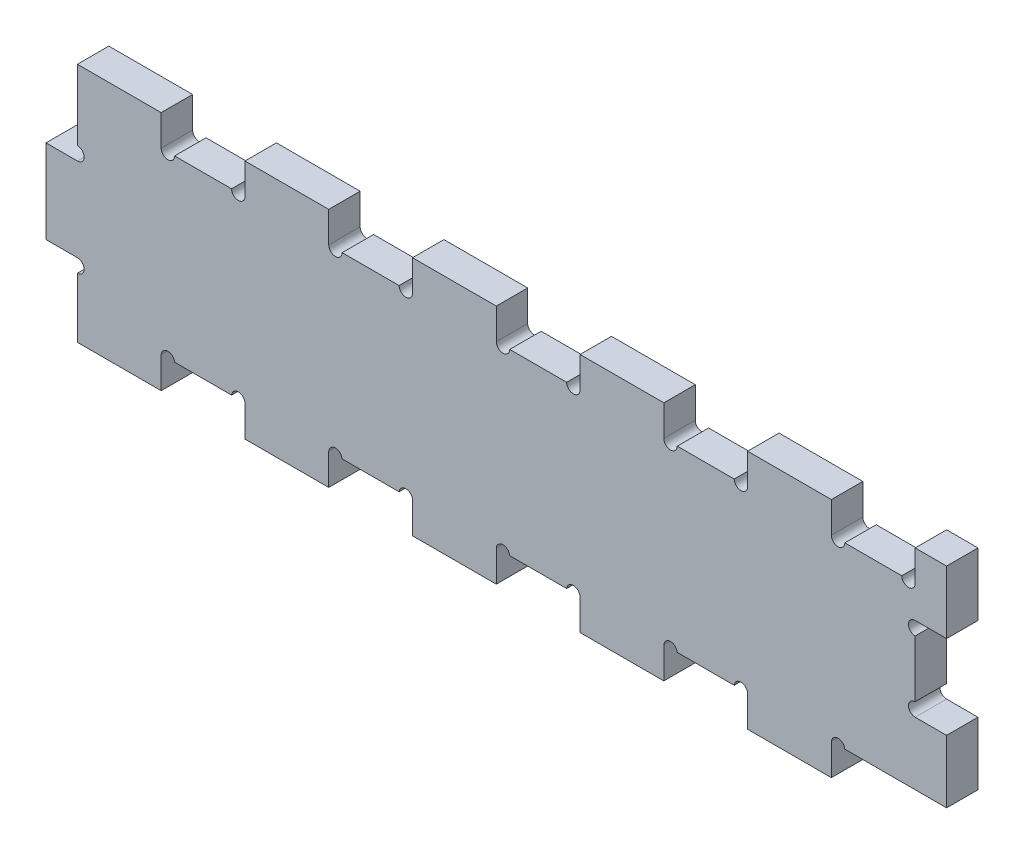
SolidWorks part; units mm, degrees
ref_plane "Alzado" through (0, 0, 0) normal (0, 0, 1) x (1, 0, 0)
ref_plane "Planta" through (0, 0, 0) normal (0, 1, 0) x (1, 0, 0)
ref_plane "Vista lateral" through (0, 0, 0) normal (1, 0, 0) x (0, 0, -1)
sketch "Croquis1" plane through (0, 0, 0) normal (0, 0, 1) x (1, 0, 0)
  line L1 (-200, -57.5) -> (-160, -57.5)
  line L2 (-215, -20) -> (-215, 20)
  line L3 (-200, 57.5) -> (-160, 57.5)
  line L5 (-215, -57.5) -> (215, 57.5) construction
  line L6 (-215, 57.5) -> (215, -57.5) construction
  line L7 (-215, 20) -> (-200, 20)
  line L9 (-215, -20) -> (-200, -20)
  line L11 (-230, 20) -> (-200, -20) construction
  line L12 (-230, -20) -> (-200, 20) construction
  line L13 (-200, 57.5) -> (-200, 26.4)
  line L14 (-160, -42.5) -> (-160, -49.3122)
  line L15 (-200, 57.5) -> (-160, 57.5)
  line L16 (-200, 57.5) -> (-200, 42.7907)
  line L18 (-160, 57.5) -> (-160, 42.7907)
  line L20 (-160, 42.7907) -> (-160, 57.5)
  line L22 (-120, 42.7907) -> (-120, 57.5)
  line L24 (-120, 42.7907) -> (-120, 57.5)
  line L25 (-120, 57.5) -> (-80, 57.5)
  line L26 (-80, 42.7907) -> (-80, 57.5)
  line L27 (-73.6, 42.7907) -> (-46.4, 42.7907)
  line L28 (-80, 42.7907) -> (-80, 57.5)
  line L30 (-40, 42.7907) -> (-40, 57.5)
  line L32 (-40, 42.7907) -> (-40, 57.5)
  line L33 (-40, 57.5) -> (0, 57.5)
  line L34 (0, 42.7907) -> (0, 57.5)
  line L36 (0, 57.5) -> (0, 42.7907)
  line L37 (6.4, 42.7907) -> (33.6, 42.7907)
  line L38 (40, 57.5) -> (40, 42.7907)
  line L40 (40, 42.7907) -> (40, 57.5)
  line L41 (40, 57.5) -> (80, 57.5)
  line L42 (80, 42.7907) -> (80, 57.5)
  line L43 (86.4, 42.7907) -> (113.6, 42.7907)
  line L44 (80, 42.7907) -> (80, 57.5)
  line L46 (120, 42.7907) -> (120, 57.5)
  line L48 (120, 42.7907) -> (120, 57.5)
  line L49 (120, 57.5) -> (160, 57.5)
  line L50 (160, 42.7907) -> (160, 57.5)
  line L51 (166.4, 42.7907) -> (193.6, 42.7907)
  line L52 (160, 42.7907) -> (160, 57.5)
  line L65 (215, 27.7907) -> (200, 27.7907)
  line L67 (215, 27.7907) -> (200, 27.7907)
  line L69 (215, -12.2093) -> (200, -12.2093)
  line L71 (200, -12.2093) -> (215, -12.2093)
  line L75 (160, -57.5) -> (120, -57.5)
  line L77 (200, -42.5) -> (166.3868, -42.5)
  line L78 (-200, -57.5) -> (-200, -42.5)
  line L79 (-120, 42.7907) -> (-120, 32.093)
  line L80 (-153.6, 42.7907) -> (-126.4, 42.7907)
  line L81 (-200, 26.4) -> (-200, 57.5)
  line L82 (-200, 23.2) -> (-200, 20)
  line L83 (40, 10.6977) -> (40, -10.6977)
  line L84 (80, 42.7907) -> (80, 21.3953)
  line L85 (120, 42.7907) -> (120, 32.093)
  line L86 (200, 42.7907) -> (200, 57.5)
  line L87 (-160, -49.3122) -> (-160, -57.5)
  line L88 (-160, -57.5) -> (-160.1599, -57.7146)
  line L89 (-80, -57.5) -> (-80, -42.5)
  line L90 (-120, -42.5) -> (-120, -57.5)
  line L91 (-40, -42.5) -> (-40, -57.5)
  line L92 (0, -42.5) -> (0, -57.5)
  line L93 (160, -42.5) -> (160, -57.5)
  line L94 (120, -42.5) -> (120, -57.5)
  line L95 (80, -42.5) -> (80, -57.5)
  line L96 (40, -42.5) -> (40, -57.5)
  line L97 (-200, -26.4) -> (-200, -57.5)
  line L98 (-120, 57.5) -> (-80, 57.5)
  line L99 (-40, 57.5) -> (0, 57.5)
  line L100 (40, 57.5) -> (80, 57.5)
  line L101 (120, 57.5) -> (160, 57.5)
  line L103 (200, -53.4884) -> (200, -57.5)
  line L105 (-120, -57.5) -> (-80, -57.5)
  line L106 (-160, -57.5) -> (-200, -57.5)
  line L107 (-120, -42.5) -> (-120.0132, -42.5)
  line L108 (-80, -57.5) -> (-120, -57.5)
  line L109 (-40, -57.5) -> (0, -57.5)
  line L110 (-40, -42.5) -> (-40.0132, -42.5)
  line L111 (0, -57.5) -> (-40, -57.5)
  line L112 (40, -57.5) -> (80, -57.5)
  line L113 (40, -42.5) -> (39.9868, -42.5)
  line L114 (80, -57.5) -> (40, -57.5)
  line L115 (120, -57.5) -> (160, -57.5)
  line L116 (120, -42.5) -> (119.9868, -42.5)
  line L117 (-200, 20) -> (-200, 23.2)
  line L118 (-215, 0) -> (-206.3098, 0)
  line L120 (-140, 42.7907) -> (-140, 32.6053)
  line L121 (-100, 57.5) -> (-100, 42.7907)
  line L122 (-20, 57.5) -> (-20, 37.3747)
  line L123 (140, 57.5) -> (140, 48.0923)
  line L124 (180, 33.8196) -> (180, 30.9199)
  line L126 (166.4, 42.7907) -> (193.6, 42.7907)
  line L127 (-158.913, -42.5) -> (-160, -42.5)
  line L128 (-126.3868, -42.5) -> (-153.6132, -42.5)
  line L129 (160, 57.5) -> (215, 57.5)
  line L130 (-79.9868, -42.5) -> (-80, -42.5)
  line L131 (-46.3868, -42.5) -> (-73.6132, -42.5)
  line L132 (0.0132, -42.5) -> (0, -42.5)
  line L133 (33.6132, -42.5) -> (6.3868, -42.5)
  line L134 (80.0132, -42.5) -> (80, -42.5)
  line L135 (113.6132, -42.5) -> (86.3868, -42.5)
  line L136 (120, -32.093) -> (120, -42.5)
  line L137 (160.0132, -42.5) -> (158.913, -42.5)
  line L141 (160, 57.5) -> (160, 42.7907)
  line L142 (200, 27.7907) -> (215, 27.7907)
  line L143 (215, 57.5) -> (215, 27.7907)
  line L144 (215, -12.2093) -> (200, -12.2093)
  line L145 (215, -12.2093) -> (215, -42.5)
  line L148 (200, -42.5) -> (215, -42.5)
  line L149 (200, -5.8093) -> (200, 21.3907)
  line L152 (200, 42.7907) -> (200, 33.8196)
  line L153 (200, 27.7907) -> (200, 24.5907)
  line L154 (200, 7.7907) -> (196.8, 7.7907)
  arc A0 (-200, 20) -> (-200, 26.4) centre (-200, 23.2) ccw
  arc A1 (-200, -20) -> (-200, -26.4) centre (-200, -23.2) cw
  arc A2 (-160, 42.7907) -> (-153.6, 42.7907) centre (-156.8, 42.7907) ccw
  arc A3 (-120, 42.7907) -> (-126.4, 42.7907) centre (-123.2, 42.7907) cw
  arc A4 (-80, 42.7907) -> (-73.6, 42.7907) centre (-76.8, 42.7907) ccw
  arc A5 (-40, 42.7907) -> (-46.4, 42.7907) centre (-43.2, 42.7907) cw
  arc A6 (120, 42.7907) -> (113.6, 42.7907) centre (116.8, 42.7907) cw
  arc A7 (80, 42.7907) -> (86.4, 42.7907) centre (83.2, 42.7907) ccw
  arc A8 (40, 42.7907) -> (33.6, 42.7907) centre (36.8, 42.7907) cw
  arc A9 (0, 42.7907) -> (6.4, 42.7907) centre (3.2, 42.7907) ccw
  arc A10 (160, 42.7907) -> (166.4, 42.7907) centre (163.2, 42.7907) ccw
  arc A13 (160, -42.7907) -> (166.3868, -42.5) centre (163.2, -42.7907) cw
  arc A14 (120, -42.7907) -> (113.6132, -42.5) centre (116.8, -42.7907) ccw
  arc A15 (80, -42.7907) -> (86.3868, -42.5) centre (83.2, -42.7907) cw
  arc A16 (40, -42.7907) -> (33.6132, -42.5) centre (36.8, -42.7907) ccw
  arc A17 (0, -42.7907) -> (6.3868, -42.5) centre (3.2, -42.7907) cw
  circle A18 centre (-43.2, -42.7907) radius 3.2
  circle A19 centre (-76.8, -42.7907) radius 3.2
  arc A20 (-120, -42.7907) -> (-126.3868, -42.5) centre (-123.2, -42.7907) ccw
  arc A21 (-160, -42.7907) -> (-153.6132, -42.5) centre (-156.8, -42.7907) cw
  arc A22 (200, 42.7907) -> (193.6, 42.7907) centre (196.8, 42.7907) cw
  arc A23 (200, 27.7907) -> (200, 21.3907) centre (200, 24.5907) ccw
  arc A24 (200, -12.2093) -> (200, -5.8093) centre (200, -9.0093) cw
  point P0 (0, 0)
  point P6 (-215, 0)
  dimension "D1" = 115
  dimension "D2" = 430
  dimension "D3" = 40
  dimension "D4" = 30
  dimension "D5" = 40
  dimension "D6" = 40
  dimension "D7" = 40
  dimension "D8" = 40
  dimension "D9" = 40
  dimension "D10" = 40
  dimension "D11" = 40
  dimension "D12" = 40
  dimension "D13" = 40
  dimension "D14" = 40
  dimension "D15" = 3.2
  dimension "D16" = 40
  dimension "D17" = 3.2
  dimension "D18" = 15
  dimension "D19" = 3.2
extrude "Saliente-Extruir2" add sketch "Croquis1" along normal blind 10
sketch "Croquis3" plane through (0, 0, 10) normal (0, 0, 1) x (1, 0, 0)
  line L59 (119.9868, -42.5) -> (120, -42.5)
  line L60 (120, -42.5) -> (120, -57.5)
  line L61 (120, -57.5) -> (160, -57.5)
  line L62 (160, -57.5) -> (160, -42.5)
  line L63 (160, -42.5) -> (160.0132, -42.5)
  line L64 (166.3868, -42.5) -> (215, -42.5)
  line L65 (215, -42.5) -> (215, -12.2093)
  line L66 (215, -12.2093) -> (200, -12.2093)
  line L67 (200, -5.8093) -> (200, 21.3907)
  line L68 (200, 27.7907) -> (215, 27.7907)
  line L69 (215, 27.7907) -> (215, 57.5)
  line L70 (215, 57.5) -> (200, 57.5)
  line L71 (200, 57.5) -> (200, 42.7907)
  line L72 (193.6, 42.7907) -> (166.4, 42.7907)
  line L73 (160, 42.7907) -> (160, 57.5)
  line L74 (160, 57.5) -> (120, 57.5)
  line L75 (120, 57.5) -> (120, 42.7907)
  line L76 (113.6, 42.7907) -> (86.4, 42.7907)
  line L77 (80, 42.7907) -> (80, 57.5)
  line L78 (80, 57.5) -> (40, 57.5)
  line L79 (40, 57.5) -> (40, 42.7907)
  line L80 (33.6, 42.7907) -> (6.4, 42.7907)
  line L81 (0, 42.7907) -> (0, 57.5)
  line L82 (0, 57.5) -> (-40, 57.5)
  line L83 (-40, 57.5) -> (-40, 42.7907)
  line L84 (-46.4, 42.7907) -> (-73.6, 42.7907)
  line L85 (-80, 42.7907) -> (-80, 57.5)
  line L86 (-80, 57.5) -> (-120, 57.5)
  line L87 (-120, 57.5) -> (-120, 42.7907)
  line L88 (-126.4, 42.7907) -> (-153.6, 42.7907)
  line L89 (-160, 42.7907) -> (-160, 57.5)
  line L90 (-160, 57.5) -> (-200, 57.5)
  line L91 (-200, 57.5) -> (-200, 26.4)
  line L92 (-200, 20) -> (-215, 20)
  line L93 (-215, 20) -> (-215, -20)
  line L94 (-215, -20) -> (-200, -20)
  line L95 (-200, -26.4) -> (-200, -57.5)
  line L96 (-200, -57.5) -> (-160, -57.5)
  line L97 (-160, -57.5) -> (-160, -42.5)
  line L98 (-160, -42.5) -> (-159.9868, -42.5)
  line L99 (-153.6132, -42.5) -> (-126.3868, -42.5)
  line L100 (-120.0132, -42.5) -> (-120, -42.5)
  line L101 (-120, -42.5) -> (-120, -57.5)
  line L102 (-120, -57.5) -> (-80, -57.5)
  line L103 (-80, -57.5) -> (-80, -42.5)
  line L104 (-80, -42.5) -> (-79.9868, -42.5)
  line L105 (-73.6132, -42.5) -> (-46.3868, -42.5)
  line L106 (-40.0132, -42.5) -> (-40, -42.5)
  line L107 (-40, -42.5) -> (-40, -57.5)
  line L108 (-40, -57.5) -> (0, -57.5)
  line L109 (0, -57.5) -> (0, -42.5)
  line L110 (0, -42.5) -> (0.0132, -42.5)
  line L111 (6.3868, -42.5) -> (33.6132, -42.5)
  line L112 (39.9868, -42.5) -> (40, -42.5)
  line L113 (40, -42.5) -> (40, -57.5)
  line L114 (40, -57.5) -> (80, -57.5)
  line L115 (80, -57.5) -> (80, -42.5)
  line L116 (80, -42.5) -> (80.0132, -42.5)
  line L117 (86.3868, -42.5) -> (113.6132, -42.5)
  line L118 (119.9868, -42.5) -> (120, -42.5)
  line L119 (120, -42.5) -> (120, -57.5)
  line L120 (120, -57.5) -> (160, -57.5)
  line L121 (160, -57.5) -> (160, -42.5)
  line L122 (160, -42.5) -> (160.0132, -42.5)
  line L123 (166.3868, -42.5) -> (215, -42.5)
  line L124 (215, -42.5) -> (215, -12.2093)
  line L125 (215, -12.2093) -> (200, -12.2093)
  line L126 (200, -5.8093) -> (200, 21.3907)
  line L127 (200, 27.7907) -> (215, 27.7907)
  line L128 (215, 27.7907) -> (215, 57.5)
  line L129 (215, 57.5) -> (200, 57.5)
  line L130 (200, 57.5) -> (200, 42.7907)
  line L131 (193.6, 42.7907) -> (166.4, 42.7907)
  line L132 (160, 42.7907) -> (160, 57.5)
  line L133 (160, 57.5) -> (120, 57.5)
  line L134 (120, 57.5) -> (120, 42.7907)
  line L135 (113.6, 42.7907) -> (86.4, 42.7907)
  line L136 (80, 42.7907) -> (80, 57.5)
  line L137 (80, 57.5) -> (40, 57.5)
  line L138 (40, 57.5) -> (40, 42.7907)
  line L139 (33.6, 42.7907) -> (6.4, 42.7907)
  line L140 (0, 42.7907) -> (0, 57.5)
  line L141 (0, 57.5) -> (-40, 57.5)
  line L142 (-40, 57.5) -> (-40, 42.7907)
  line L143 (-46.4, 42.7907) -> (-73.6, 42.7907)
  line L144 (-80, 42.7907) -> (-80, 57.5)
  line L145 (-80, 57.5) -> (-120, 57.5)
  line L146 (-120, 57.5) -> (-120, 42.7907)
  line L147 (-126.4, 42.7907) -> (-153.6, 42.7907)
  line L148 (-160, 42.7907) -> (-160, 57.5)
  line L149 (-160, 57.5) -> (-200, 57.5)
  line L150 (-200, 57.5) -> (-200, 26.4)
  line L151 (-200, 20) -> (-215, 20)
  line L152 (-215, 20) -> (-215, -20)
  line L153 (-215, -20) -> (-200, -20)
  line L154 (-200, -26.4) -> (-200, -57.5)
  line L155 (-200, -57.5) -> (-160, -57.5)
  line L156 (-160, -57.5) -> (-160, -42.5)
  line L157 (-160, -42.5) -> (-159.9868, -42.5)
  line L158 (-153.6132, -42.5) -> (-126.3868, -42.5)
  line L159 (-120.0132, -42.5) -> (-120, -42.5)
  line L160 (-120, -42.5) -> (-120, -57.5)
  line L161 (-120, -57.5) -> (-80, -57.5)
  line L162 (-80, -57.5) -> (-80, -42.5)
  line L163 (-80, -42.5) -> (-79.9868, -42.5)
  line L164 (-73.6132, -42.5) -> (-46.3868, -42.5)
  line L165 (-40.0132, -42.5) -> (-40, -42.5)
  line L166 (-40, -42.5) -> (-40, -57.5)
  line L167 (-40, -57.5) -> (0, -57.5)
  line L168 (0, -57.5) -> (0, -42.5)
  line L169 (0, -42.5) -> (0.0132, -42.5)
  line L170 (6.3868, -42.5) -> (33.6132, -42.5)
  line L171 (39.9868, -42.5) -> (40, -42.5)
  line L172 (40, -42.5) -> (40, -57.5)
  line L173 (40, -57.5) -> (80, -57.5)
  line L174 (80, -57.5) -> (80, -42.5)
  line L175 (80, -42.5) -> (80.0132, -42.5)
  line L176 (86.3868, -42.5) -> (113.6132, -42.5)
  arc A23 (166.3868, -42.5) -> (160.0132, -42.5) centre (163.2, -42.7907) ccw
  arc A24 (200, -5.8093) -> (200, -12.2093) centre (200, -9.0093) ccw
  arc A25 (200, 27.7907) -> (200, 21.3907) centre (200, 24.5907) ccw
  arc A26 (193.6, 42.7907) -> (200, 42.7907) centre (196.8, 42.7907) ccw
  arc A27 (160, 42.7907) -> (166.4, 42.7907) centre (163.2, 42.7907) ccw
  arc A28 (113.6, 42.7907) -> (120, 42.7907) centre (116.8, 42.7907) ccw
  arc A29 (80, 42.7907) -> (86.4, 42.7907) centre (83.2, 42.7907) ccw
  arc A30 (33.6, 42.7907) -> (40, 42.7907) centre (36.8, 42.7907) ccw
  arc A31 (0, 42.7907) -> (6.4, 42.7907) centre (3.2, 42.7907) ccw
  arc A32 (-46.4, 42.7907) -> (-40, 42.7907) centre (-43.2, 42.7907) ccw
  arc A33 (-80, 42.7907) -> (-73.6, 42.7907) centre (-76.8, 42.7907) ccw
  arc A34 (-126.4, 42.7907) -> (-120, 42.7907) centre (-123.2, 42.7907) ccw
  arc A35 (-160, 42.7907) -> (-153.6, 42.7907) centre (-156.8, 42.7907) ccw
  arc A36 (-200, 20) -> (-200, 26.4) centre (-200, 23.2) ccw
  arc A37 (-200, -26.4) -> (-200, -20) centre (-200, -23.2) ccw
  arc A38 (-153.6132, -42.5) -> (-159.9868, -42.5) centre (-156.8, -42.7907) ccw
  arc A39 (-120.0132, -42.5) -> (-126.3868, -42.5) centre (-123.2, -42.7907) ccw
  arc A40 (-73.6132, -42.5) -> (-79.9868, -42.5) centre (-76.8, -42.7907) ccw
  arc A41 (-40.0132, -42.5) -> (-46.3868, -42.5) centre (-43.2, -42.7907) ccw
  arc A42 (6.3868, -42.5) -> (0.0132, -42.5) centre (3.2, -42.7907) ccw
  arc A43 (39.9868, -42.5) -> (33.6132, -42.5) centre (36.8, -42.7907) ccw
  arc A44 (86.3868, -42.5) -> (80.0132, -42.5) centre (83.2, -42.7907) ccw
  arc A45 (119.9868, -42.5) -> (113.6132, -42.5) centre (116.8, -42.7907) ccw
  arc A46 (166.3868, -42.5) -> (160.0132, -42.5) centre (163.2, -42.7907) ccw
  arc A47 (200, -5.8093) -> (200, -12.2093) centre (200, -9.0093) ccw
  arc A48 (200, 27.7907) -> (200, 21.3907) centre (200, 24.5907) ccw
  arc A49 (193.6, 42.7907) -> (200, 42.7907) centre (196.8, 42.7907) ccw
  arc A50 (160, 42.7907) -> (166.4, 42.7907) centre (163.2, 42.7907) ccw
  arc A51 (113.6, 42.7907) -> (120, 42.7907) centre (116.8, 42.7907) ccw
  arc A52 (80, 42.7907) -> (86.4, 42.7907) centre (83.2, 42.7907) ccw
  arc A53 (33.6, 42.7907) -> (40, 42.7907) centre (36.8, 42.7907) ccw
  arc A54 (0, 42.7907) -> (6.4, 42.7907) centre (3.2, 42.7907) ccw
  arc A55 (-46.4, 42.7907) -> (-40, 42.7907) centre (-43.2, 42.7907) ccw
  arc A56 (-80, 42.7907) -> (-73.6, 42.7907) centre (-76.8, 42.7907) ccw
  arc A57 (-126.4, 42.7907) -> (-120, 42.7907) centre (-123.2, 42.7907) ccw
  arc A58 (-160, 42.7907) -> (-153.6, 42.7907) centre (-156.8, 42.7907) ccw
  arc A59 (-200, 20) -> (-200, 26.4) centre (-200, 23.2) ccw
  arc A60 (-200, -26.4) -> (-200, -20) centre (-200, -23.2) ccw
  arc A61 (-153.6132, -42.5) -> (-159.9868, -42.5) centre (-156.8, -42.7907) ccw
  arc A62 (-120.0132, -42.5) -> (-126.3868, -42.5) centre (-123.2, -42.7907) ccw
  arc A63 (-73.6132, -42.5) -> (-79.9868, -42.5) centre (-76.8, -42.7907) ccw
  arc A64 (-40.0132, -42.5) -> (-46.3868, -42.5) centre (-43.2, -42.7907) ccw
  arc A65 (6.3868, -42.5) -> (0.0132, -42.5) centre (3.2, -42.7907) ccw
  arc A66 (39.9868, -42.5) -> (33.6132, -42.5) centre (36.8, -42.7907) ccw
  arc A67 (86.3868, -42.5) -> (80.0132, -42.5) centre (83.2, -42.7907) ccw
  arc A68 (119.9868, -42.5) -> (113.6132, -42.5) centre (116.8, -42.7907) ccw
  dimension "D1" = 0
extrude "Saliente-Extruir3" add sketch "Croquis3" along normal blind 5
sketch "Croquis4" plane through (0, 0, 15) normal (0, 0, 1) x (1, 0, 0)
  line L0 (-215, 20) -> (-215, -20) construction
  line L1 (-200, 57.5) -> (-215, 57.5)
  line L2 (-200, 57.5) -> (-200, 17.5)
  line L3 (-200, 17.5) -> (-215, 17.5)
  line L4 (-215, 57.5) -> (-215, 17.5)
  dimension "D1" = 40
extrude "Cortar-Extruir1" cut sketch "Croquis4" against normal blind 15
sketch "Croquis5" plane through (0, 0, 15) normal (0, 0, 1) x (1, 0, 0)
  line L0 (-200, -26.4) -> (-200, -57.5) construction
  line L1 (-215, 17.5) -> (-200, 17.5)
  line L2 (-215, 17.5) -> (-215, -22.5)
  line L3 (-215, -22.5) -> (-200, -22.5)
  line L4 (-200, 17.5) -> (-200, -22.5)
  dimension "D1" = 40
extrude "Saliente-Extruir4" add sketch "Croquis5" against normal blind 15
sketch "Croquis6" plane through (0, 0, 15) normal (0, 0, 1) x (1, 0, 0)
  line L0 (-200, -22.5) -> (-200, -20) construction
  line L1 (-200, -22.5) -> (-200, -20)
  line L2 (-200, -26.4) -> (-200, -22.5)
  line L3 (-200, 20) -> (-200, 26.4)
  arc A0 (-200, -26.4) -> (-200, -20) centre (-200, -23.2) ccw construction
  arc A1 (-200, 20) -> (-200, 26.4) centre (-200, 23.2) ccw construction
  arc A2 (-200, -26.4) -> (-200, -20) centre (-200, -23.2) ccw
  arc A3 (-200, 20) -> (-200, 26.4) centre (-200, 23.2) ccw
extrude "Saliente-Extruir5" add sketch "Croquis6" against normal blind 15
sketch "Croquis7" plane through (0, 0, 15) normal (0, 0, 1) x (1, 0, 0)
  line L0 (-200, 17.5) -> (-200, 20.7)
  line L1 (-200, 57.5) -> (-200, 17.5) construction
  line L2 (-200, -22.5) -> (-200, -25.7)
  line L3 (-200, -22.5) -> (-200, -57.5) construction
  circle A0 centre (-200, 20.7) radius 3.2
  circle A1 centre (-200, -25.7) radius 3.2
  dimension "D1" = 3.2
  dimension "D2" = 3.2
extrude "Cortar-Extruir2" cut sketch "Croquis7" against normal blind 15
sketch "Croquis8" plane through (0, 0, 15) normal (0, 0, 1) x (1, 0, 0)
  line L1 (215, 57.5) -> (200, 57.5)
  line L2 (215, 57.5) -> (215, 27.5)
  line L3 (215, 27.5) -> (200, 27.5)
  line L4 (200, 57.5) -> (200, 27.5)
  dimension "D1" = 30
extrude "Saliente-Extruir6" add sketch "Croquis8" against normal blind 15
sketch "Croquis9" plane through (0, 0, 15) normal (0, 0, 1) x (1, 0, 0)
  line L1 (215, 27.5) -> (200, 27.5)
  line L2 (215, 27.5) -> (215, -12.5)
  line L3 (215, -12.5) -> (200, -12.5)
  line L4 (200, 27.5) -> (200, -12.5)
  dimension "D1" = 15
  dimension "D2" = 40
extrude "Cortar-Extruir3" cut sketch "Croquis9" against normal blind 15
sketch "Croquis10" plane through (0, 0, 15) normal (0, 0, 1) x (1, 0, 0)
  line L0 (200, -5.8093) -> (200, -12.2093)
  line L1 (200, 27.5) -> (200, 21.3907)
  line L2 (200, 27.7907) -> (200, 27.5) construction
  line L3 (200, 27.7907) -> (200, 27.5)
  arc A0 (200, 27.7907) -> (200, 21.3907) centre (200, 24.5907) ccw construction
  arc A1 (200, 27.7907) -> (200, 21.3907) centre (200, 24.5907) ccw
  arc A2 (200, -5.8093) -> (200, -12.2093) centre (200, -9.0093) ccw construction
  arc A3 (200, -5.8093) -> (200, -12.2093) centre (200, -9.0093) ccw
extrude "Saliente-Extruir8" add sketch "Croquis10" against normal blind 15
sketch "Croquis12" plane through (0, 0, 15) normal (0, 0, 1) x (1, 0, 0)
  line L0 (200, 27.5) -> (200, 24.3)
  line L1 (200, -12.5) -> (200, 27.5) construction
  line L2 (200, -12.5) -> (200, -9.3)
  circle A0 centre (200, 24.3) radius 3.2
  circle A1 centre (200, -9.3) radius 3.2
  dimension "D1" = 3.2
  dimension "D2" = 3.2
extrude "Cortar-Extruir4" cut sketch "Croquis12" against normal blind 15
